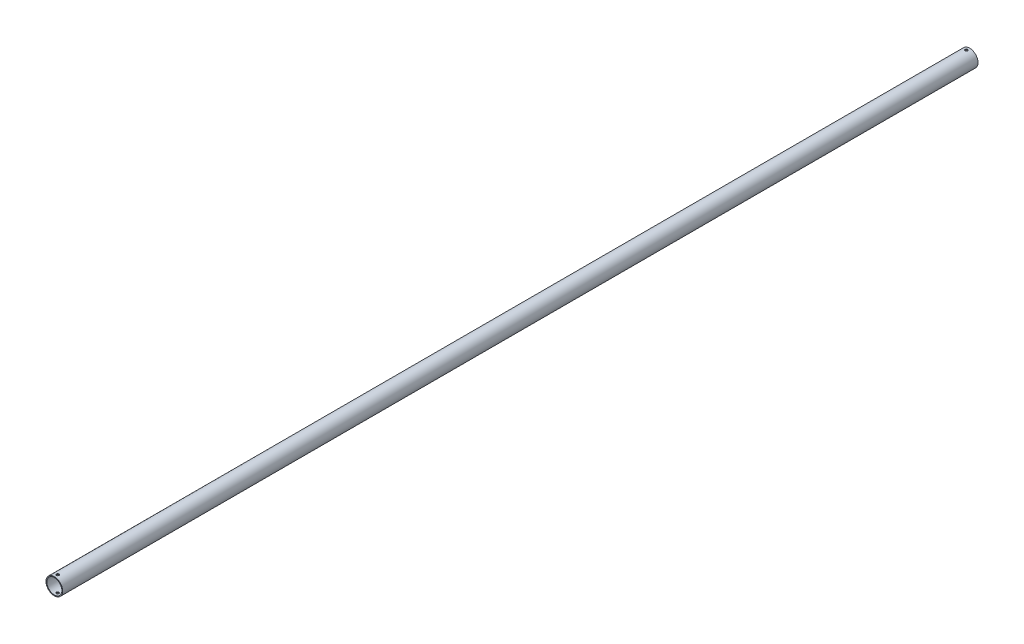
SolidWorks part; units mm, degrees
ref_plane "Front Plane" through (0, 0, 0) normal (0, 0, 1) x (1, 0, 0)
ref_plane "Top Plane" through (0, 0, 0) normal (0, 1, 0) x (1, 0, 0)
ref_plane "Right Plane" through (0, 0, 0) normal (1, 0, 0) x (0, 0, -1)
sketch "Sketch1" plane through (0, 0, 0) normal (0, 0, 1) x (1, 0, 0)
  circle A0 centre (0, 0) radius 15.875
  circle A1 centre (0, 0) radius 14.2875
  dimension "D1" = 31.75
extrude "Boss-Extrude1" add sketch "Sketch1" along normal blind 1739.9
ref_plane "Plane1" through (0, 0, 1739.9) normal (0, 0, 1) x (1, 0, 0)
hole_wizard "#10 (0.1935) Diameter Hole1" positions "3DSketch3" profile "Sketch3" hole size "#10" standard "ANSI Inch" end condition through all
sketch3d "3DSketch3"
  point P0 (0, -15.875, 6.35)
  dimension "D1" = 6.35
sketch "Sketch3" plane through (0, -15.875, 6.35) normal (1, 0, 0) x (0, 0, -1)
  line L0 (0, 0) -> (0, 31.75)
  line L1 (0, 31.75) -> (2.4574, 31.75)
  line L2 (2.4574, 31.75) -> (2.4574, 0)
  line L5 (2.4574, 0) -> (0, 0)
  line L11 (0, -6.35) -> (0, 107.95) construction
  dimension "Thru Hole Dia." = 4.9149
  dimension "Thru Hole Depth" = 31.75
hole_wizard "#10 (0.1935) Diameter Hole2" positions "3DSketch4" profile "Sketch4" hole size "#10" standard "ANSI Inch" end condition through all
sketch3d "3DSketch4"
  point P0 (0, 15.875, 1733.55)
  dimension "D1" = 6.35
sketch "Sketch4" plane through (0, 15.875, 1733.55) normal (1, 0, 0) x (0, 0, 1)
  line L0 (0, 0) -> (0, 31.75)
  line L1 (0, 31.75) -> (2.4574, 31.75)
  line L2 (2.4574, 31.75) -> (2.4574, 0)
  line L5 (2.4574, 0) -> (0, 0)
  line L11 (0, -6.35) -> (0, 107.95) construction
  dimension "Thru Hole Dia." = 4.9149
  dimension "Thru Hole Depth" = 31.75
equation "\"D1@Boss-Extrude1\"=108*2"
